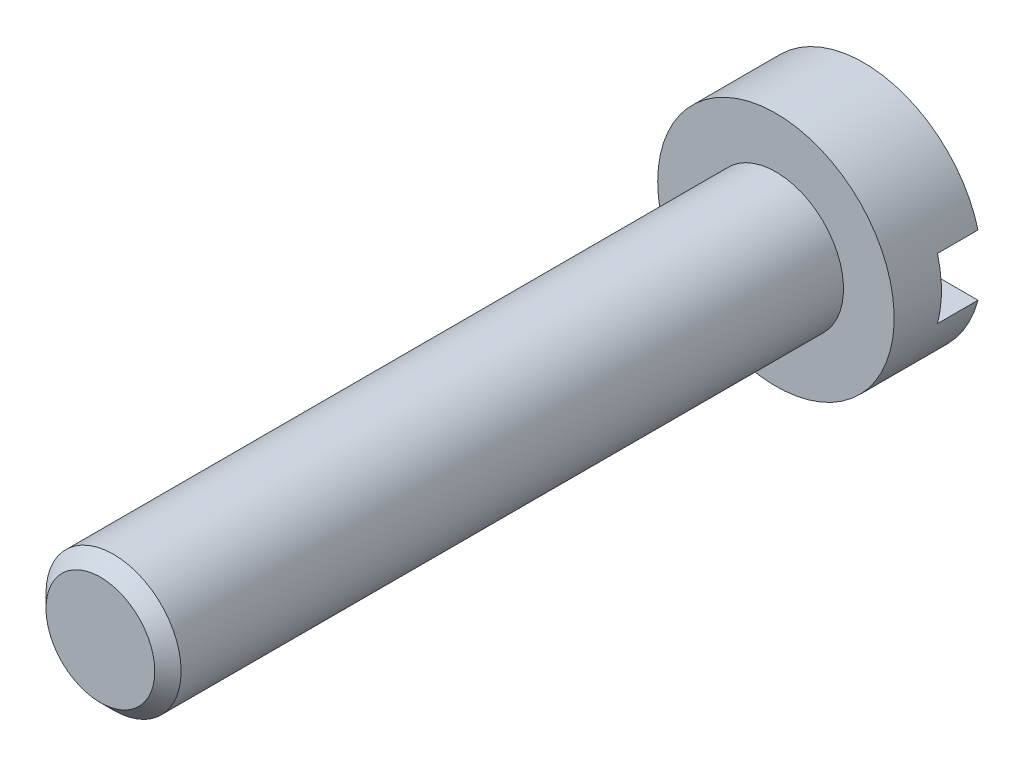
SolidWorks part; units mm, degrees
material "Сталь"
ref_plane "Спереди" through (0, 0, 0) normal (0, 0, 1) x (1, 0, 0)
ref_plane "Сверху" through (0, 0, 0) normal (0, 1, 0) x (1, 0, 0)
ref_plane "Справа" through (0, 0, 0) normal (1, 0, 0) x (0, 0, -1)
sketch "Эскиз1" plane through (0, 0, 0) normal (0, 0, 1) x (1, 0, 0)
  circle A0 centre (0, 0) radius 2
  dimension "D1" = 4
extrude "Бобышка-Вытянуть1" add sketch "Эскиз1" along normal blind 20
cosmetic thread "Условное изображение резьбы1" parameters "D1"=14, "D2"=3.22
sketch "Эскиз2" plane through (0, 0, 0) normal (0, 0, -1) x (-1, 0, 0)
  circle A0 centre (0, 0) radius 3.5
  dimension "D1" = 7
extrude "Бобышка-Вытянуть2" add sketch "Эскиз2" along normal blind 2.6
sketch "Эскиз3" plane through (0, 0, -2.6) normal (0, 0, -1) x (-1, 0, 0)
  line L1 (-4.5, 0.9) -> (4.5, 0.9)
  line L2 (-4.5, 0.9) -> (-4.5, -0.9)
  line L3 (-4.5, -0.9) -> (4.5, -0.9)
  line L4 (4.5, 0.9) -> (4.5, -0.9)
  line L5 (-4.5, 0.9) -> (4.5, -0.9) construction
  line L6 (-4.5, -0.9) -> (4.5, 0.9) construction
  point P0 (0, 0)
  dimension "D1" = 1.8
  dimension "D2" = 9
extrude "Вырез-Вытянуть1" cut sketch "Эскиз3" against normal blind 1.2
chamfer "Фаска1" distance 0.39 angle 45 1 edges at (2, 0, 20)
